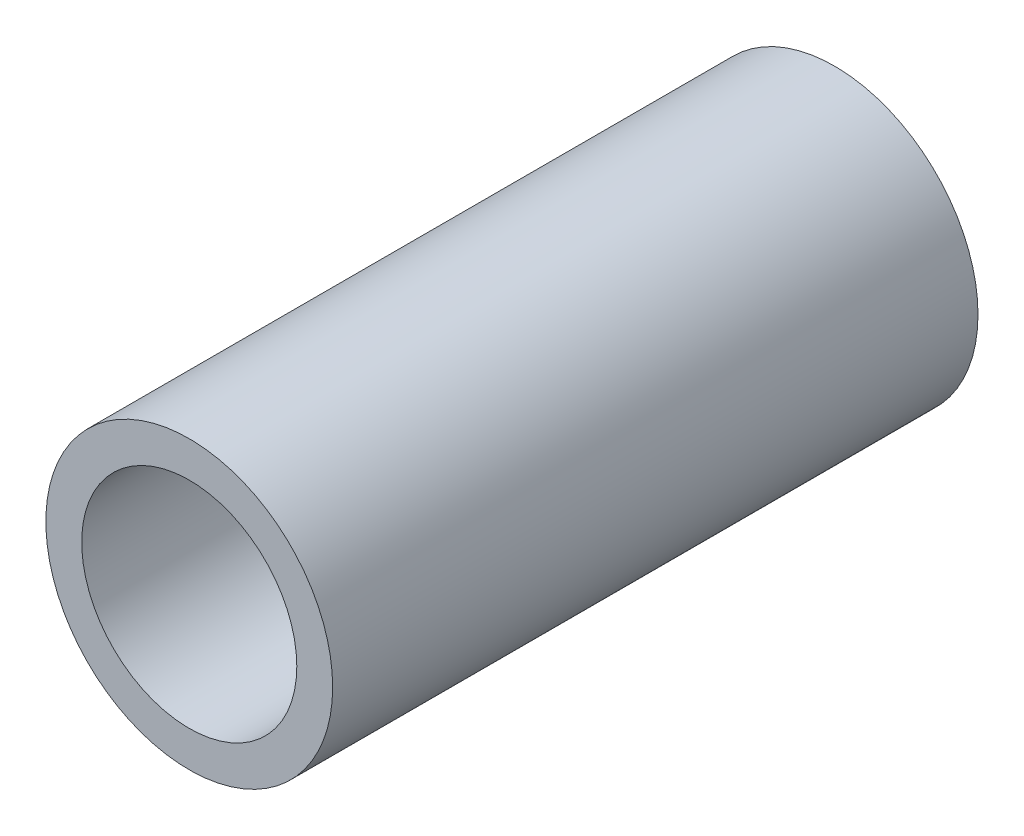
SolidWorks part; units mm, degrees
ref_plane "Front" through (0, 0, 0) normal (0, 0, 1) x (1, 0, 0)
ref_plane "Top" through (0, 0, 0) normal (0, 1, 0) x (1, 0, 0)
ref_plane "Right" through (0, 0, 0) normal (1, 0, 0) x (0, 0, -1)
sketch "草图1" plane through (0, 0, 0) normal (0, 0, 1) x (1, 0, 0)
  circle A0 centre (0, 0) radius 1.5
  circle A1 centre (0, 0) radius 2
  dimension "D1" = 4
  dimension "D2" = 3
extrude "凸台-拉伸1" add sketch "草图1" along normal blind 9
